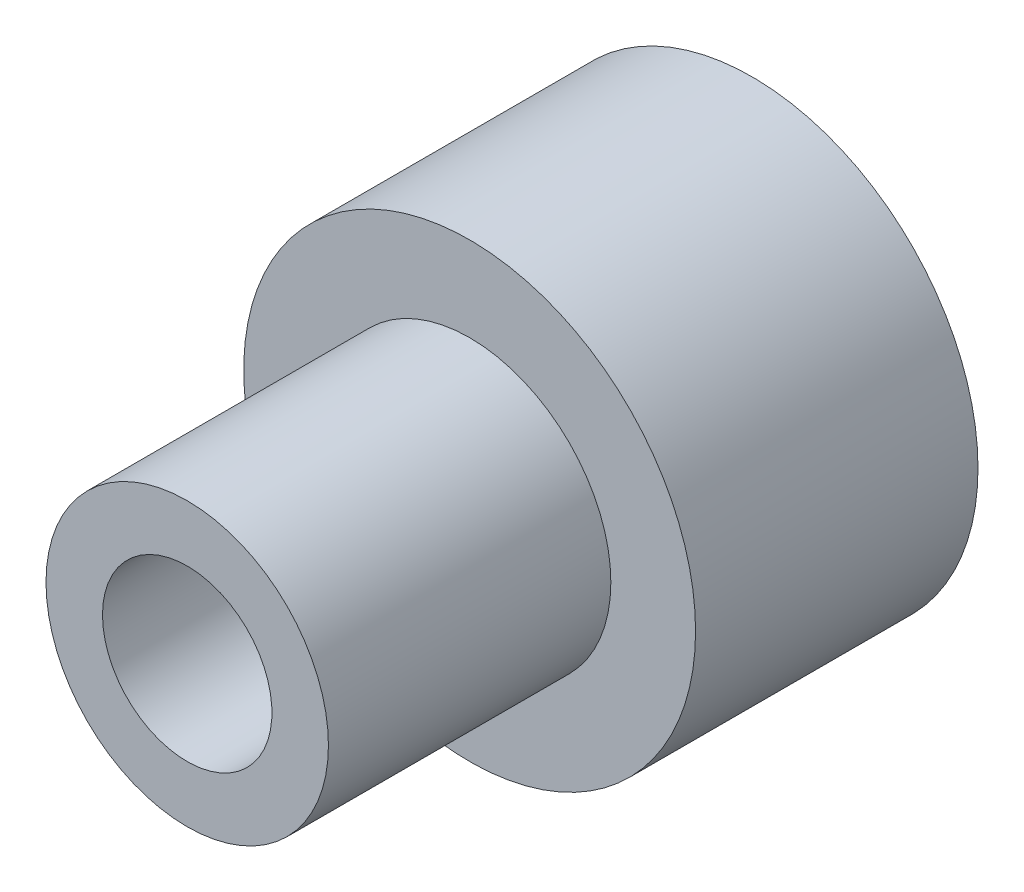
SolidWorks part; units mm, degrees
ref_plane "Front Plane" through (0, 0, 0) normal (0, 0, 1) x (1, 0, 0)
ref_plane "Top Plane" through (0, 0, 0) normal (0, 1, 0) x (1, 0, 0)
ref_plane "Right Plane" through (0, 0, 0) normal (1, 0, 0) x (0, 0, -1)
sketch "Sketch1" plane through (0, 0, 0) normal (0, 0, 1) x (1, 0, 0)
  circle A0 centre (0, 0) radius 4
  dimension "D1" = 8
extrude "Boss-Extrude1" add sketch "Sketch1" along normal blind 5
sketch "Sketch2" plane through (0, 0, 5) normal (0, 0, 1) x (1, 0, 0)
  circle A0 centre (0, 0) radius 2.5
  dimension "D1" = 5
extrude "Boss-Extrude2" add sketch "Sketch2" along normal blind 5
sketch "Sketch4" plane through (0, 0, 0) normal (0, 0, -1) x (-1, 0, 0)
  circle A0 centre (0, 0) radius 1.5
  dimension "D1" = 3
extrude "Cut-Extrude2" cut sketch "Sketch4" against normal blind 10
